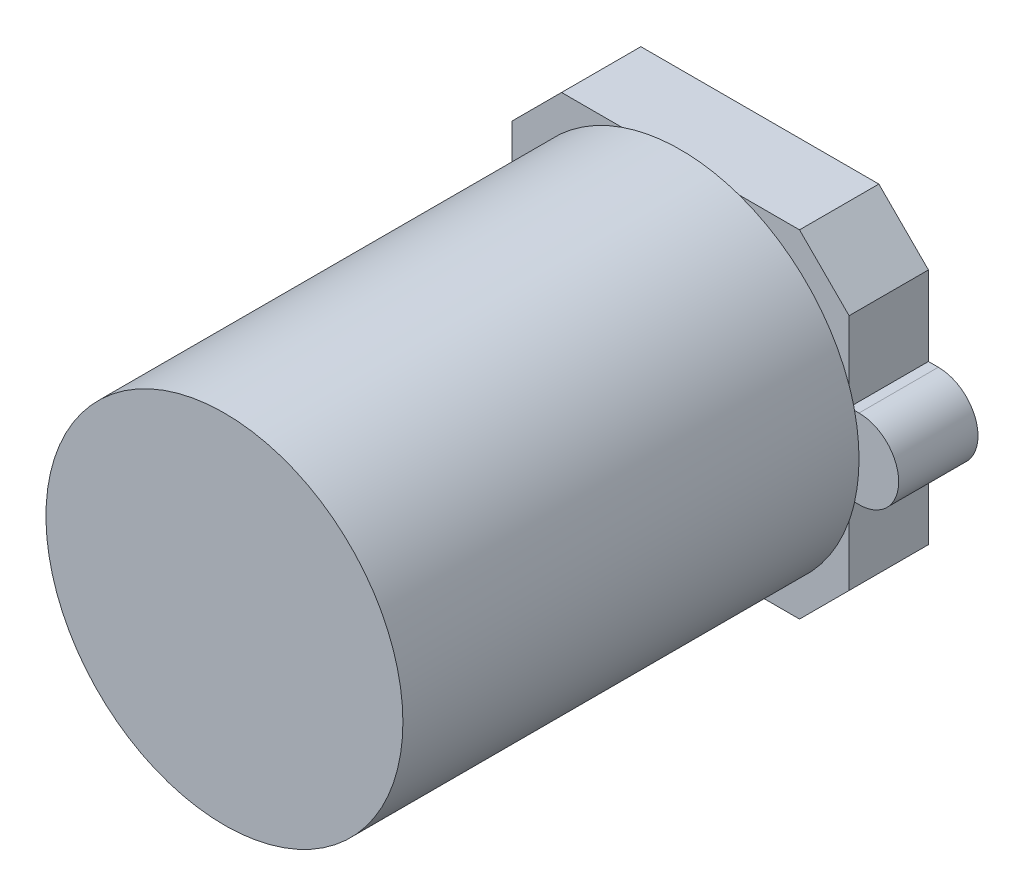
SolidWorks part; units mm, degrees
ref_plane "Front Plane" through (0, 0, 0) normal (0, 0, 1) x (1, 0, 0)
ref_plane "Top Plane" through (0, 0, 0) normal (0, 1, 0) x (1, 0, 0)
ref_plane "Right Plane" through (0, 0, 0) normal (1, 0, 0) x (0, 0, -1)
sketch "Sketch1" plane through (0, 0, 0) normal (0, 0, 1) x (1, 0, 0)
  line L1 (-8.5, -8.5) -> (8.5, -8.5)
  line L2 (-8.5, -8.5) -> (-8.5, 8.5)
  line L3 (-8.5, 8.5) -> (8.5, 8.5)
  line L4 (8.5, -8.5) -> (8.5, 8.5)
  line L5 (-8.5, -8.5) -> (8.5, 8.5) construction
  line L6 (-8.5, 8.5) -> (8.5, -8.5) construction
  point P0 (0, 0)
  dimension "D1" = 17
  dimension "D2" = 17
extrude "Boss-Extrude1" add sketch "Sketch1" along normal blind 4
chamfer "Chamfer1" distance 2.5 angle 45 5 edges at (8.5, -8.5, 2) (-8.5, -8.5, 2) (0, 8.5, 0) (-8.5, 8.5, 2) (8.5, 8.5, 2)
sketch "Sketch3" plane through (0, 0, 0) normal (0, 0, 1) x (1, 0, 0)
  line L0 (-8.5, 2) -> (-9, 2)
  line L1 (-8.5, 6) -> (-8.5, -6) construction
  line L2 (-9, -2) -> (-8.5, -2)
  line L3 (-8.5, -2) -> (-8.5, 2)
  arc A0 (-9, 2) -> (-9, -2) centre (-9, 0) ccw
  dimension "D1" = 4
  dimension "D2" = 2
  dimension "D3" = 0.5
extrude "Boss-Extrude3" add sketch "Sketch3" along normal up to surface (4 mm away) up to face at (0, 0, 4)
mirror "Mirror1" about plane through (0, 0, 0) normal (1, 0, 0) of "Boss-Extrude3"
sketch "Sketch2" plane through (0, 0, 4) normal (0, 0, 1) x (1, 0, 0)
  circle A0 centre (0, 0) radius 9
  dimension "D1" = 18
extrude "Boss-Extrude2" add sketch "Sketch2" along normal blind 23
sketch "Sketch4" plane through (0, 0, 27) normal (0, 0, 1) x (1, 0, 0)
  point P0 (0, 0)
